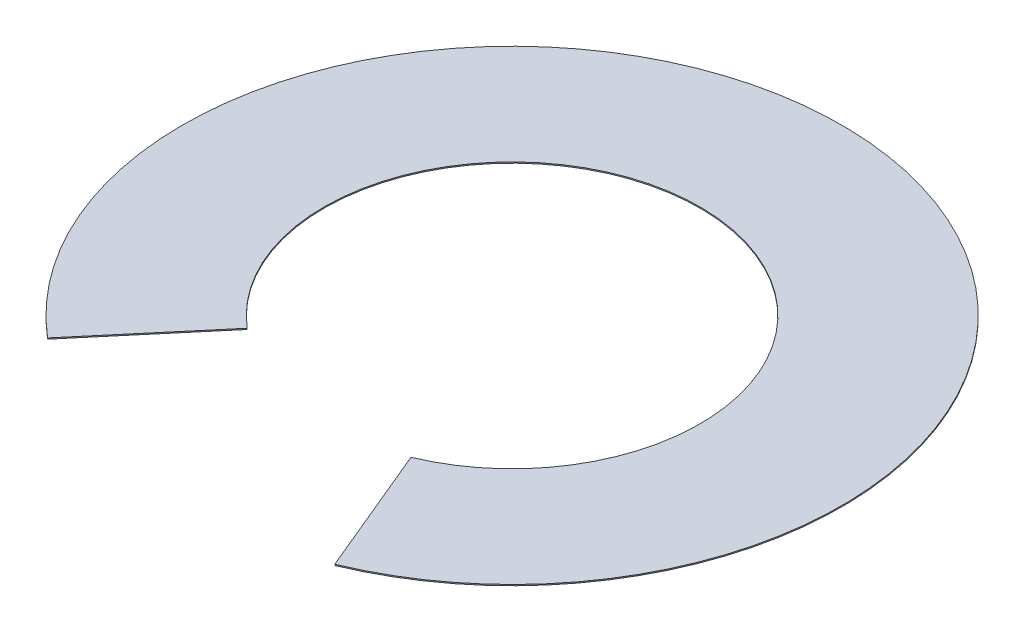
SolidWorks part; units mm, degrees
ref_plane "Front Plane" through (0, 0, 0) normal (0, 0, 1) x (1, 0, 0)
ref_plane "Top Plane" through (0, 0, 0) normal (0, 1, 0) x (1, 0, 0)
ref_plane "Right Plane" through (0, 0, 0) normal (1, 0, 0) x (0, 0, -1)
sketch "Sketch1" plane through (0, 0, 0) normal (0, 1, 0) x (1, 0, 0)
  line L2 (-172.9575, -204.7186) -> (-303.321, -359.0214)
  line L3 (103.1763, -247.3432) -> (180.9435, -433.7735)
  arc A0 (180.9435, -433.7735) -> (-303.321, -359.0214) centre (0, 0) ccw
  arc A1 (103.1763, -247.3432) -> (-172.9575, -204.7186) centre (0, 0) ccw
  dimension "D1" = 940
  dimension "D2" = 202
  dimension "D3" = 490
extrude "Boss-Extrude1" add sketch "Sketch1" along normal blind 1.6
